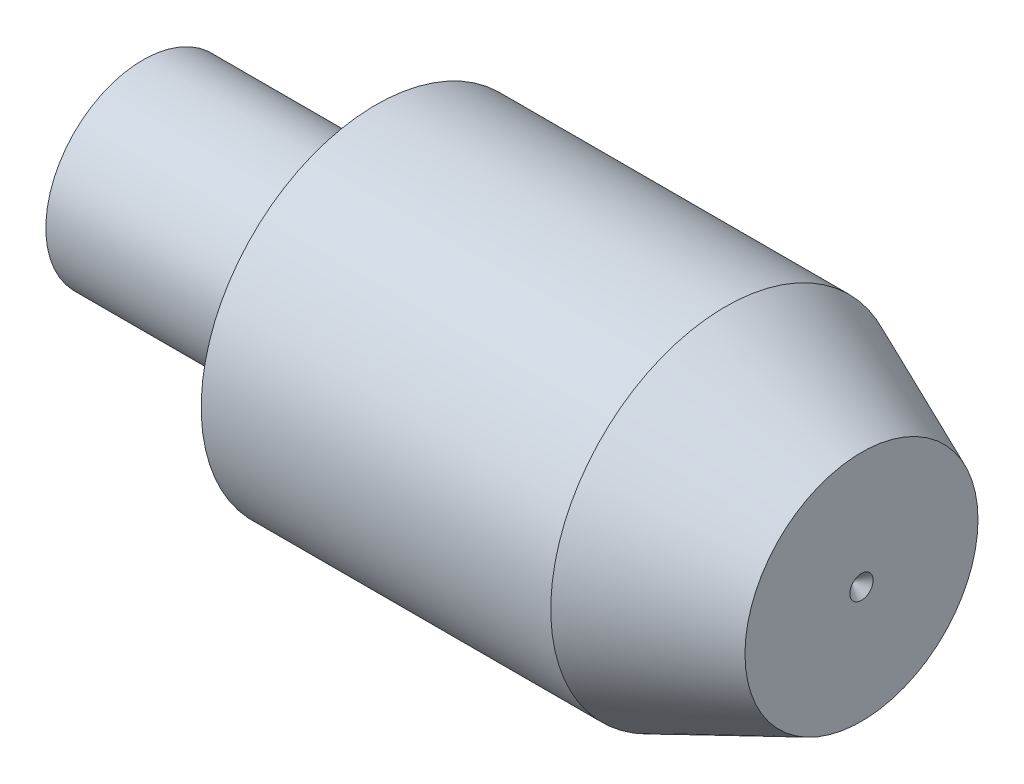
SolidWorks part; units mm, degrees
ref_plane "前视基准面" through (0, 0, 0) normal (0, 0, 1) x (1, 0, 0)
ref_plane "上视基准面" through (0, 0, 0) normal (0, 1, 0) x (1, 0, 0)
ref_plane "右视基准面" through (0, 0, 0) normal (1, 0, 0) x (0, 0, -1)
sketch "草图1" plane through (0, 0, 0) normal (0, 0, 1) x (1, 0, 0)
  line L0 (0, 5) -> (0, 9)
  line L1 (0, -55) -> (0, 55) construction
  line L2 (0, 9) -> (18, 9)
  line L3 (25, 6) -> (25, 0)
  line L4 (55, 0) -> (-55, 0) construction
  line L5 (25, 0) -> (0, 0)
  line L6 (18, 9) -> (25, 6)
  line L7 (0, 5) -> (-12, 5)
  line L8 (-12, 5) -> (-12, 0)
  line L9 (-12, 0) -> (0, 0)
  point P6 (25, 9)
  dimension "D1" = 9
  dimension "D2" = 25
  dimension "D3" = 7
  dimension "D4" = 3
  dimension "D5" = 12
  dimension "D6" = 5
revolve "旋转1" add sketch "草图1" angle 360 about L5
cosmetic thread "装饰螺纹线1" parameters "D2"=6.647
sketch "草图2" plane through (25, 0, 0) normal (1, 0, 0) x (0, 0, -1)
  line L0 (0, 9.9) -> (0, -9.9) construction
  circle A0 centre (0, 0) radius 0.6
  dimension "D1" = 1.2
extrude "切除-拉伸1" cut sketch "草图2" against normal blind 0.6 draft 45
